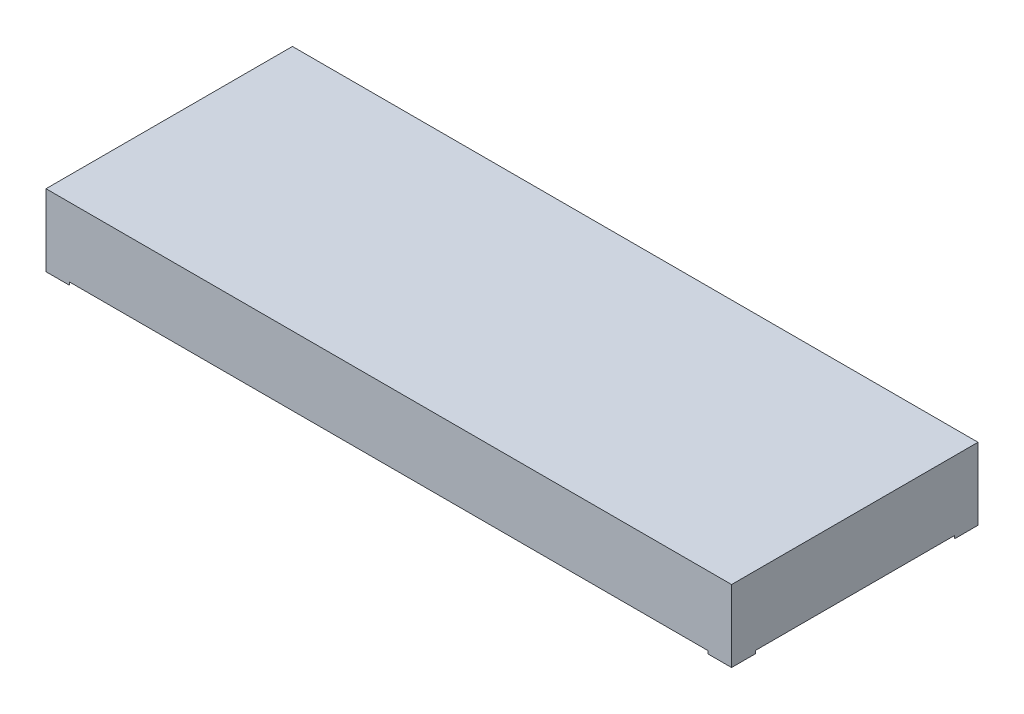
SolidWorks part; units mm, degrees
ref_plane "前视基准面" through (0, 0, 0) normal (0, 0, 1) x (1, 0, 0)
ref_plane "上视基准面" through (0, 0, 0) normal (0, 1, 0) x (1, 0, 0)
ref_plane "右视基准面" through (0, 0, 0) normal (1, 0, 0) x (0, 0, -1)
sketch "草图1" plane through (0, 0, 0) normal (0, 1, 0) x (1, 0, 0)
  line L1 (0, 0) -> (71.5, 0)
  line L2 (0, 0) -> (0, -25.7)
  line L3 (0, -25.7) -> (71.5, -25.7)
  line L4 (71.5, 0) -> (71.5, -25.7)
  dimension "D1" = 25.7
  dimension "D2" = 71.5
extrude "凸台-拉伸1" add sketch "草图1" along normal blind 7.5
sketch "草图2" plane through (0, 0, 0) normal (0, -1, 0) x (1, 0, 0)
  line L0 (35.75, 25.7) -> (35.75, -7.3244) construction
  line L1 (0, 25.7) -> (71.5, 25.7) construction
  line L2 (0, 12.85) -> (77.0908, 12.85) construction
  line L3 (0, 0) -> (0, 25.7) construction
  line L4 (2.4749, 25.7) -> (0, 23.2251)
  line L5 (0, 23.2251) -> (0, 25.7)
  line L6 (0, 25.7) -> (2.4749, 25.7)
  line L7 (0, 0) -> (2.4749, 0)
  line L8 (0, 2.4749) -> (0, 0)
  line L9 (2.4749, 0) -> (0, 2.4749)
  line L10 (71.5, 25.7) -> (69.0251, 25.7)
  line L11 (71.5, 23.2251) -> (71.5, 25.7)
  line L12 (69.0251, 25.7) -> (71.5, 23.2251)
  line L13 (69.0251, 0) -> (71.5, 2.4749)
  line L14 (71.5, 2.4749) -> (71.5, 0)
  line L15 (71.5, 0) -> (69.0251, 0)
  line L16 (2.4749, 25.7) -> (69.0251, 25.7)
  line L17 (71.5, 23.2251) -> (71.5, 2.4749)
  line L18 (69.0251, 0) -> (2.4749, 0)
  line L19 (0, 23.2251) -> (0, 2.4749)
  line M6 (0, 25.7) -> (0, 0)
  line M7 (0, 0) -> (71.5, 0)
  line M8 (71.5, 0) -> (71.5, 25.7)
  line M9 (71.5, 25.7) -> (0, 25.7)
  dimension "D1" = 3.5
extrude "切除-拉伸1" cut sketch "草图2" against normal blind 0.3 contours L13 L12 L4 L9 M7 M8 M9 M6
